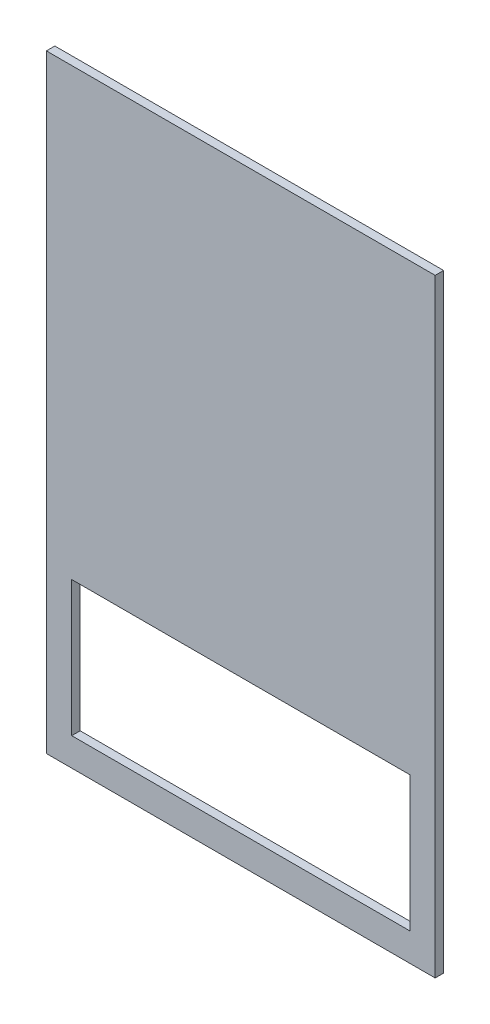
SolidWorks part; units mm, degrees
ref_plane "Front Plane" through (0, 0, 0) normal (0, 0, 1) x (1, 0, 0)
ref_plane "Top Plane" through (0, 0, 0) normal (0, 1, 0) x (1, 0, 0)
ref_plane "Right Plane" through (0, 0, 0) normal (1, 0, 0) x (0, 0, -1)
sketch "Sketch1" plane through (0, 0, 0) normal (0, 0, 1) x (1, 0, 0)
  line L1 (-292.1, -457.2) -> (292.1, -457.2)
  line L2 (-292.1, -457.2) -> (-292.1, 457.2)
  line L3 (-292.1, 457.2) -> (292.1, 457.2)
  line L4 (292.1, -457.2) -> (292.1, 457.2)
  line L5 (-292.1, -457.2) -> (292.1, 457.2) construction
  line L6 (-292.1, 457.2) -> (292.1, -457.2) construction
  point P0 (0, 0)
  dimension "D1" = 584.2
  dimension "D2" = 914.4
extrude "Boss-Extrude1" add sketch "Sketch1" along normal blind 12.7
sketch "Sketch2" plane through (0, 0, 12.7) normal (0, 0, 1) x (1, 0, 0)
  line L0 (-292.1, -414.909) -> (0, -414.909) construction
  line L1 (-292.1, 457.2) -> (-292.1, -457.2) construction
  line L2 (-292.1, -457.2) -> (292.1, -457.2) construction
  line L4 (0, -414.909) -> (0, -313.309) construction
  line L9 (0, 0) -> (0, -414.909) construction
  line L11 (254, -211.709) -> (-254, -211.709)
  line L12 (254, -211.709) -> (254, -414.909)
  line L13 (254, -414.909) -> (-254, -414.909)
  line L14 (-254, -211.709) -> (-254, -414.909)
  line L15 (254, -211.709) -> (-254, -414.909) construction
  line L16 (254, -414.909) -> (-254, -211.709) construction
  dimension "D1" = 101.6
  dimension "D2" = 42.291
  dimension "D3" = 508
extrude "Cut-Extrude1" cut sketch "Sketch2" against normal through all
